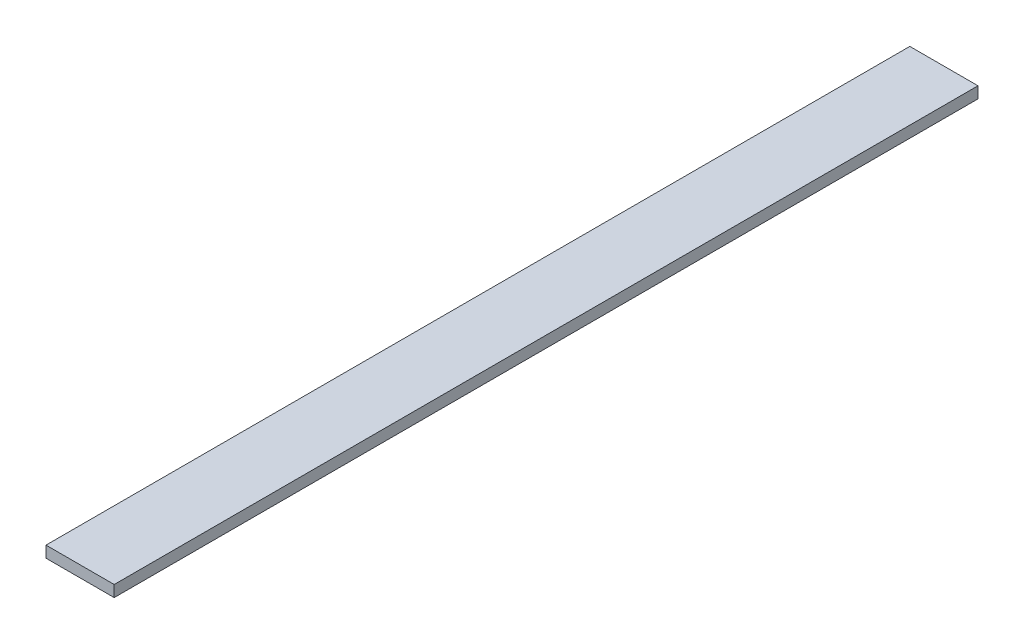
SolidWorks part; units mm, degrees
material "Plywood"
ref_plane "Front Plane" through (0, 0, 0) normal (0, 0, 1) x (1, 0, 0)
ref_plane "Top Plane" through (0, 0, 0) normal (0, 1, 0) x (1, 0, 0)
ref_plane "Right Plane" through (0, 0, 0) normal (1, 0, 0) x (0, 0, -1)
sketch "Sketch1" plane through (0, 0, 0) normal (0, 0, 1) x (1, 0, 0)
  line L1 (0, 0) -> (19.05, 0)
  line L2 (0, 0) -> (0, 3.175)
  line L3 (0, 3.175) -> (19.05, 3.175)
  line L4 (19.05, 0) -> (19.05, 3.175)
  dimension "D1" = 19.05
  dimension "D2" = 3.175
extrude "Boss-Extrude1" add sketch "Sketch1" along normal blind 241.3
move or copy body "Body-Move/Copy1" [suppressed] bodies to move or copy 101 parameters "D1"=0, "D2"=0, "D3"=0
